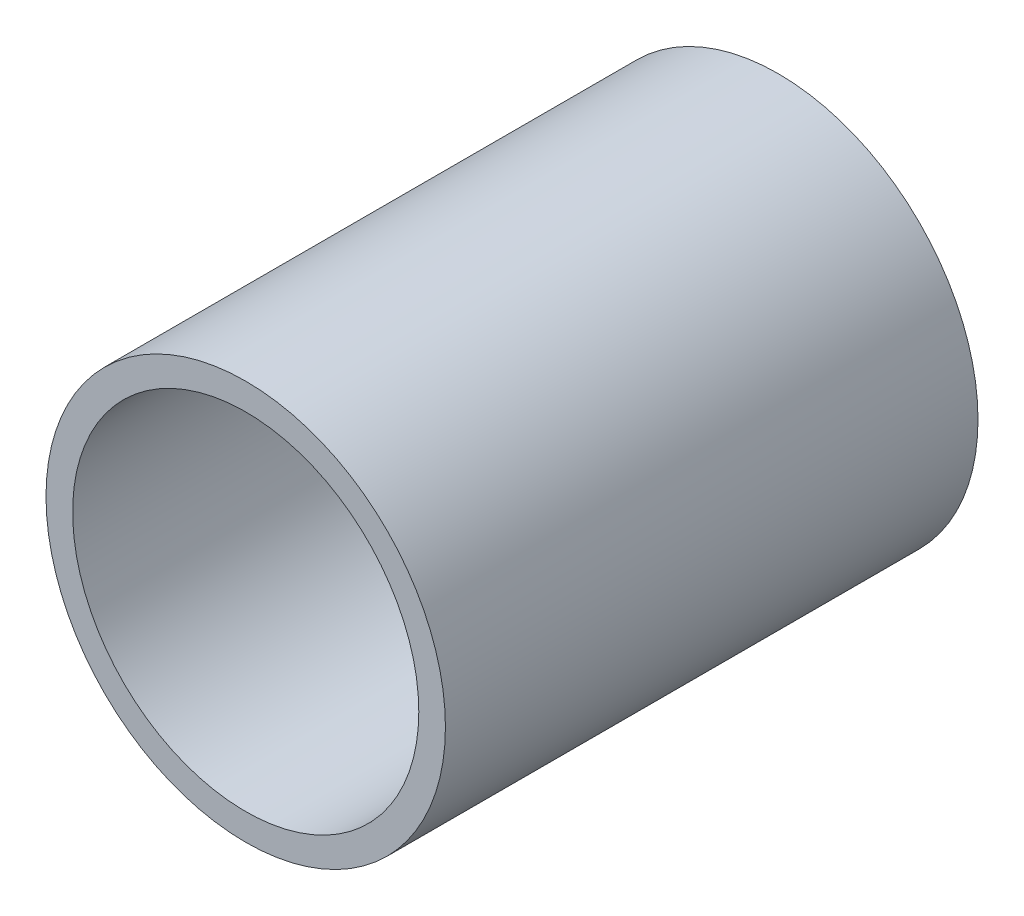
SolidWorks part; units mm, degrees
ref_plane "Plano frontal" through (0, 0, 0) normal (0, 0, 1) x (1, 0, 0)
ref_plane "Plano superior" through (0, 0, 0) normal (0, 1, 0) x (1, 0, 0)
ref_plane "Plano direito" through (0, 0, 0) normal (1, 0, 0) x (0, 0, -1)
sketch "Esboço1" plane through (0, 0, 0) normal (0, 0, 1) x (1, 0, 0)
  circle A0 centre (0, 0) radius 7.5
  circle A1 centre (0, 0) radius 6.5
  point P4 (0, 6.5)
  point P5 (0, 7.5)
  dimension "D1" = 15
  dimension "D2" = 1
extrude "Ressalto-extrusão1" add sketch "Esboço1" along normal blind 20
